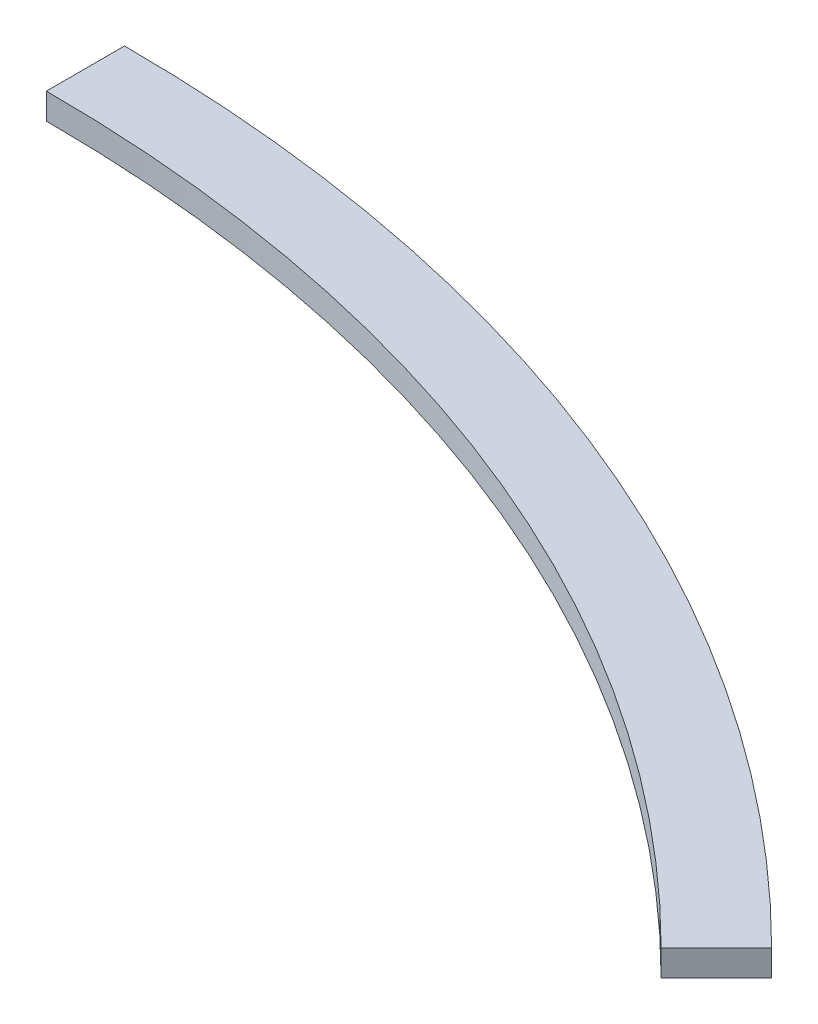
SolidWorks part; units mm, degrees
ref_plane "Front Plane" through (0, 0, 0) normal (0, 0, 1) x (1, 0, 0)
ref_plane "Top Plane" through (0, 0, 0) normal (0, 1, 0) x (1, 0, 0)
ref_plane "Right Plane" through (0, 0, 0) normal (1, 0, 0) x (0, 0, -1)
sketch "Sketch1" plane through (0, 0, 0) normal (0, 1, 0) x (1, 0, 0)
  line L0 (0, 0) -> (0, 570) construction
  line L1 (0, 570) -> (0, 600)
  line L2 (0, 0) -> (424.2641, 424.2641) construction
  line L3 (403.0509, 403.0509) -> (424.2641, 424.2641)
  arc A0 (0, 570) -> (403.0509, 403.0509) centre (0, 0) cw
  arc A1 (0, 600) -> (424.2641, 424.2641) centre (0, 0) cw
  dimension "D1" = 30
  dimension "D2" = 570
  dimension "D3" = 600
  dimension "D4" = 45
extrude "Boss-Extrude1" add sketch "Sketch1" along normal blind 10
